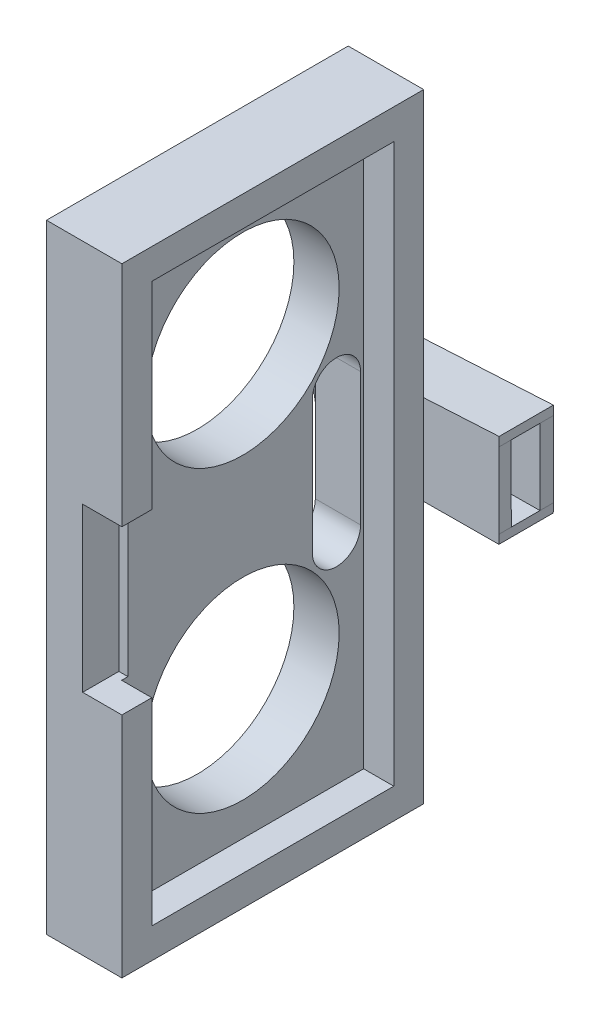
SolidWorks part; units mm, degrees
ref_plane "Front Plane" through (0, 0, 0) normal (0, 0, 1) x (1, 0, 0)
ref_plane "Top Plane" through (0, 0, 0) normal (0, 1, 0) x (1, 0, 0)
ref_plane "Right Plane" through (0, 0, 0) normal (1, 0, 0) x (0, 0, -1)
sketch "Sketch1" plane through (0, 0, 0) normal (0, 0, 1) x (1, 0, 0)
  line L0 (-14.1591, -1.997) -> (-2.2091, -2.65) construction
  line L1 (-2.2091, 2.65) -> (-14.1591, 1.997) construction
  line L4 (-14.1591, 2.5058) -> (-2.2211, 3.1581)
  line L5 (-14.1471, -3.2624) -> (-2.2091, -3.1919)
  line L10 (-2.2211, 3.9201) -> (-14.1591, 3.2678)
  line L11 (-2.2347, -3.9539) -> (-14.1727, -4.0244)
  line L12 (-2.2347, -3.9539) -> (-2.2091, -3.1919)
  line L13 (-2.2211, 3.1581) -> (-2.2211, 3.9201)
  arc A2 (-14.1591, 2.5058) -> (-14.1471, -3.2624) centre (-14.1591, -0.3783) ccw
  arc A4 (-14.1591, 3.2678) -> (-14.1727, -4.0244) centre (-14.1591, -0.3783) ccw
  point P9 (0, 0)
  dimension "D2" = 11.938
  dimension "D8" = 0.762
  dimension "D1" = 0.508
  dimension "D3" = 11.938
  dimension "D4" = 11.938
  dimension "D5" = 11.938
  dimension "D6" = 0.762
  dimension "D7" = 0.762
  dimension "D9" = 6.35
extrude "Boss-Extrude1" add sketch "Sketch1" along normal blind 1.524 and the other way blind 3.048 contours L10 A4 L11 L12 L5 A2 L4 L13
sketch "Sketch2" plane through (0, 0, 1.524) normal (0, 0, 1) x (1, 0, 0)
  line L0 (-2.2091, -3.1919) -> (-2.2211, 3.1581)
  line L6 (-2.2211, 3.9201) -> (-14.1591, 3.2678)
  line L7 (-14.1025, -4.024) -> (-2.2347, -3.9539)
  line L8 (-2.2347, -3.9539) -> (-2.2091, -3.1919)
  line L9 (-2.2091, -3.1919) -> (-14.1471, -3.2624)
  line L10 (-14.1591, 2.5058) -> (-2.2211, 3.1581)
  line L11 (-2.2211, 3.1581) -> (-2.2211, 3.9201)
  line L15 (-2.2091, -3.1919) -> (-14.1471, -3.2624)
  line L16 (-14.1591, 2.5058) -> (-2.2211, 3.1581)
  arc A2 (-14.1591, 3.2678) -> (-14.1025, -4.024) centre (-14.1591, -0.3783) ccw
  arc A3 (-14.1591, 2.5058) -> (-14.1471, -3.2624) centre (-14.1591, -0.3783) ccw
  arc A5 (-14.1591, 2.5058) -> (-14.1471, -3.2624) centre (-14.1591, -0.3783) ccw
  dimension "D1" = 0
extrude "Boss-Extrude2" add sketch "Sketch2" against normal blind 1.016
sketch "Sketch3" plane through (0, 0, -3.048) normal (0, 0, -1) x (-1, 0, 0)
  line L0 (14.1591, 2.5058) -> (2.2211, 3.1581) construction
  line L1 (14.1471, -3.2624) -> (2.2091, -3.1919) construction
  line L2 (14.1591, 2.5058) -> (2.2211, 3.1581)
  line L3 (14.1471, -3.2624) -> (2.2091, -3.1919)
  line L4 (2.2091, -3.1919) -> (2.2211, 3.1581)
  arc A0 (14.1471, -3.2624) -> (14.1591, 2.5058) centre (14.1591, -0.3783) ccw construction
  arc A1 (14.1471, -3.2624) -> (14.1591, 2.5058) centre (14.1591, -0.3783) ccw
extrude "Boss-Extrude3" add sketch "Sketch3" against normal blind 1.143
sketch "Sketch4" plane through (0, 0, 1.524) normal (0, 0, 1) x (1, 0, 0)
  line L1 (-14.9201, 26.035) -> (-8.5701, 26.035)
  line L2 (-14.9201, 26.035) -> (-14.9201, -26.035)
  line L3 (-14.9201, -26.035) -> (-8.5701, -26.035)
  line L4 (-8.5701, 26.035) -> (-8.5701, -26.035)
  point P4 (-14.9201, 0)
  dimension "D1" = 6.35
  dimension "D2" = 52.07
extrude "Boss-Extrude4" add sketch "Sketch4" along normal blind 25.4
sketch "Sketch5" plane through (-8.5701, 0, 0) normal (1, 0, 0) x (0, 0, -1)
  line L0 (-26.924, -26.035) -> (-1.524, -26.035) construction
  line L1 (-24.4094, -23.495) -> (-4.0386, -23.495)
  line L2 (-24.4094, -23.495) -> (-24.4094, 23.495)
  line L3 (-24.4094, 23.495) -> (-4.0386, 23.495)
  line L4 (-4.0386, -23.495) -> (-4.0386, 23.495)
  line L5 (-26.924, -26.035) -> (-26.924, 26.035) construction
  line L7 (-26.924, 26.035) -> (-1.524, 26.035) construction
  line L8 (-1.524, 3.5732) -> (-1.524, 26.035) construction
  dimension "D1" = 2.54
  dimension "D2" = 2.5146
  dimension "D3" = 2.54
  dimension "D4" = 2.5146
extrude "Cut-Extrude1" cut sketch "Sketch5" against normal blind 2.54
sketch "Sketch6" plane through (-11.1101, 0, 0) normal (1, 0, 0) x (0, 0, -1)
  line L0 (-26.924, 26.035) -> (-1.524, 26.035) construction
  line L1 (-26.924, -26.035) -> (-1.524, -26.035) construction
  circle A0 centre (-14.224, -12.573) radius 8.128
  circle A1 centre (-14.224, 12.573) radius 8.128
  point P6 (-14.224, 26.035)
  point P7 (0, 0)
  point P8 (0, 0)
  dimension "D1" = 16.256
  dimension "D2" = 16.256
  dimension "D4" = 13.462
  dimension "D3" = 13.462
extrude "Cut-Extrude2" cut sketch "Sketch6" against normal through all
sketch "Sketch7" plane through (0, 0, 26.924) normal (0, 0, 1) x (1, 0, 0)
  line L0 (-8.5701, -26.035) -> (-8.5701, 26.035) construction
  line L1 (-11.8721, -6.858) -> (-8.5701, -6.858)
  line L2 (-11.8721, -6.858) -> (-11.8721, 6.858)
  line L3 (-11.8721, 6.858) -> (-8.5701, 6.858)
  line L4 (-8.5701, -6.858) -> (-8.5701, 6.858)
  line L5 (-14.9201, 26.035) -> (-14.9201, -26.035) construction
  dimension "D1" = 6.858
  dimension "D2" = 6.858
  dimension "D3" = 3.048
extrude "Cut-Extrude3" cut sketch "Sketch7" against normal blind 3.048
sketch "Sketch8" plane through (-11.1101, 0, 0) normal (1, 0, 0) x (0, 0, -1)
  line L0 (-6.3246, -5.588) -> (-6.3246, 5.588) construction
  line L1 (-8.3566, -5.588) -> (-8.3566, 5.588)
  line L2 (-4.2926, -5.588) -> (-4.2926, 5.588)
  line L4 (-4.0386, -23.495) -> (-4.0386, 23.495) construction
  arc A0 (-8.3566, -5.588) -> (-4.2926, -5.588) centre (-6.3246, -5.588) ccw
  arc A1 (-4.2926, 5.588) -> (-8.3566, 5.588) centre (-6.3246, 5.588) ccw
  point P2 (-6.3246, 0)
  dimension "D1" = 0.254
  dimension "D2" = 11.176
  dimension "D3" = 4.064
extrude "Cut-Extrude4" cut sketch "Sketch8" against normal blind 3.81
